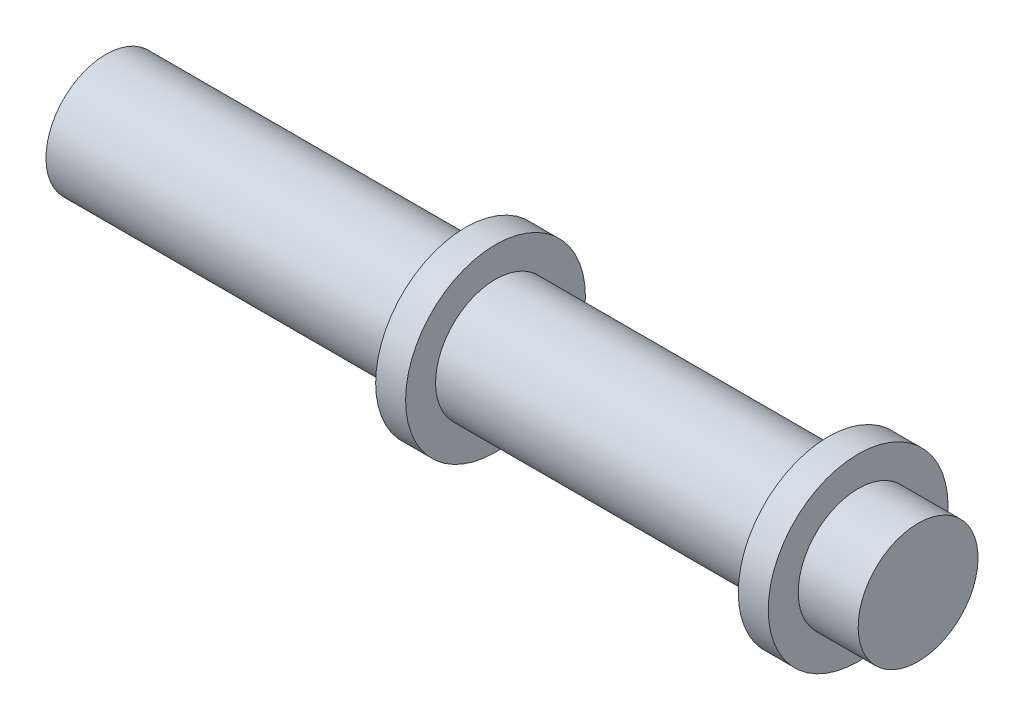
SolidWorks part; units mm, degrees
ref_plane "Front Plane" through (0, 0, 0) normal (0, 0, 1) x (1, 0, 0)
ref_plane "Top Plane" through (0, 0, 0) normal (0, 1, 0) x (1, 0, 0)
ref_plane "Right Plane" through (0, 0, 0) normal (1, 0, 0) x (0, 0, -1)
sketch "Sketch2" plane through (0, 0, 0) normal (0, 0, 1) x (1, 0, 0)
  line L0 (-27.1, 4) -> (-3.1, 4)
  line L1 (-3.1, 4) -> (-3.1, 6)
  line L2 (-3.1, 6) -> (-1.1, 6)
  line L3 (-1.1, 6) -> (-1.1, 4)
  line L4 (-1.1, 4) -> (21.1, 4)
  line L6 (27.1, 0) -> (-27.1, 0)
  line L7 (-27.1, 0) -> (-27.1, 4)
  line L8 (27.1, 0) -> (27.1, 4)
  line L11 (21.1, 4) -> (21.1, 6)
  line L12 (21.1, 6) -> (23.1, 6)
  line L13 (23.1, 4) -> (23.1, 6)
  line L14 (23.1, 4) -> (27.1, 4)
  point P2 (0, 0)
  dimension "D1" = 4
  dimension "D2" = 2
  dimension "D3" = 2
  dimension "D4" = 2
  dimension "D5" = 26.2
  dimension "D6" = 4
  dimension "D7" = 24
revolve "Revolve1" add sketch "Sketch2" angle 360 about L6
